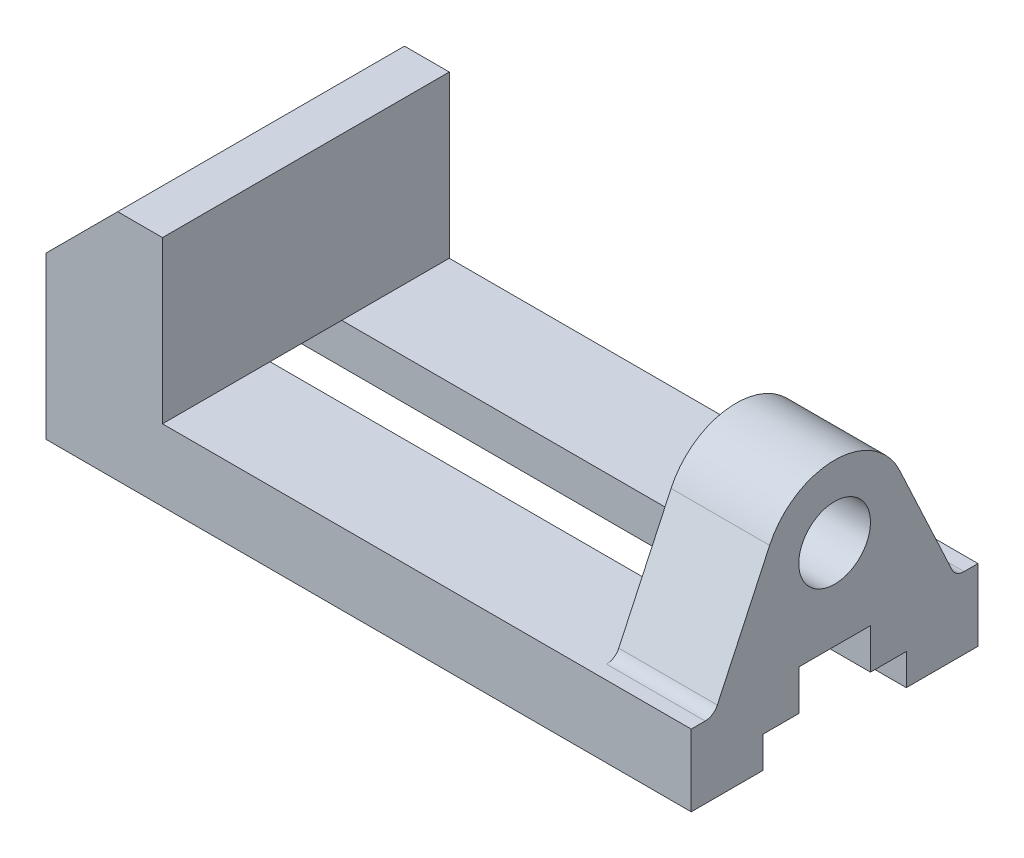
SolidWorks part; units mm, degrees
ref_plane "Front Plane" through (0, 0, 0) normal (0, 0, 1) x (1, 0, 0)
ref_plane "Top Plane" through (0, 0, 0) normal (0, 1, 0) x (1, 0, 0)
ref_plane "Right Plane" through (0, 0, 0) normal (1, 0, 0) x (0, 0, -1)
sketch "Sketch1" plane through (0, 0, 0) normal (0, 0, 1) x (1, 0, 0)
  line L0 (0, 0) -> (0, 36)
  line L1 (0, 36) -> (16, 52)
  line L2 (16, 52) -> (26, 52)
  line L3 (26, 52) -> (26, 16)
  line L4 (26, 16) -> (144, 16)
  line L5 (144, 16) -> (144, 0)
  line L6 (0, 0) -> (144, 0)
  point P4 (0, 36.9833)
  dimension "D1" = 144
  dimension "D2" = 16
  dimension "D3" = 36
  dimension "D4" = 16
  dimension "D5" = 16
  dimension "D6" = 10
extrude "Boss-Extrude1" add sketch "Sketch1" along normal mid plane 64
sketch "Sketch3" plane through (144, 0, 0) normal (1, 0, 0) x (0, 0, -1)
  line L0 (-32, 52) -> (32, 52) construction
  line L1 (-32, 16) -> (32, 16) construction
  line L2 (-32, 16) -> (-28.8914, 16)
  line L3 (-14.5009, 42.7619) -> (-26.1725, 17.7321)
  line L4 (-32, 0) -> (32, 0) construction
  line L5 (14.5009, 42.7619) -> (26.1725, 17.7321)
  line L6 (0, 67.4933) -> (0, -9.7095) construction
  line L8 (28.8914, 16) -> (32, 16)
  line L9 (-28.8914, 16) -> (28.8914, 16)
  circle A0 centre (0, 36) radius 8
  arc A1 (14.5009, 42.7619) -> (-14.5009, 42.7619) centre (0, 36) ccw
  arc A2 (-26.1725, 17.7321) -> (-28.8914, 16) centre (-28.8914, 19) cw
  arc A3 (26.1725, 17.7321) -> (28.8914, 16) centre (28.8914, 19) ccw
  point P21 (26.9802, 16)
  line M6 (32, 16) -> (-32, 16)
  dimension "D1" = 32
  dimension "D2" = 16
  dimension "D7" = 3
  dimension "D8" = 3
  dimension "D3" = 36
  dimension "D4" = 50
  dimension "D5" = 25
  dimension "D6" = 16
extrude "Boss-Extrude2" add sketch "Sketch3" against normal blind 22 contours L6 A1 L3 A2 L9 A0 | A1 L6 A0 A3 L5 M6
sketch "Sketch4" plane through (144, 0, 0) normal (1, 0, 0) x (0, 0, -1)
  line L0 (-16, 0) -> (16, 0)
  line L1 (-32, 0) -> (32, 0) construction
  line L2 (-16, 7) -> (-8, 7)
  line L3 (-16, 0) -> (-16, 7)
  line L4 (16, 0) -> (16, 7)
  line L5 (-8, 16) -> (8, 16)
  line L6 (-8, 7) -> (-8, 16)
  line L7 (8, 16) -> (8, 7)
  line L8 (8, 7) -> (16, 7)
  point P6 (0, 0)
  point P10 (0, 16)
  dimension "D1" = 32
  dimension "D3" = 16
  dimension "D4" = 16
  dimension "D5" = 16
  dimension "D6" = 32
extrude "Cut-Extrude1" cut sketch "Sketch4" against normal through all
hole_wizard "Ø6.0mm Dowel Hole1" positions "Sketch5" profile "Sketch6" hole size "Ø6.0" standard "ISO"
sketch "Sketch5" plane through (0, 0, 0) normal (0, -1, 0) x (-1, 0, 0)
  line L0 (0, -32) -> (-144, -32) construction
  line L1 (0, -32) -> (0, -16) construction
  point P0 (-38, -22)
  dimension "D1" = 10
  dimension "D2" = 38
sketch "Sketch6" plane through (38, 0, 22) normal (1, 0, 0) x (0, 0, -1)
  line L0 (0, 0) -> (0, 11.8026)
  line L1 (0, 11.8026) -> (3, 10)
  line L2 (3, 10) -> (3, 0)
  line L5 (3, 0) -> (0, 0)
  line L10 (0, 11.8026) -> (-3, 10) construction
  line L11 (0, -6.35) -> (0, 107.95) construction
  dimension "Hole Dia." = 6
  dimension "Hole Depth" = 10
  dimension "Drill Angle" = 118
pattern_linear "LPattern1" count 2 spacing 70 along (1, 0, 0) count 2 spacing 44 along (0, 0, -1) of "Ø6.0mm Dowel Hole1"
